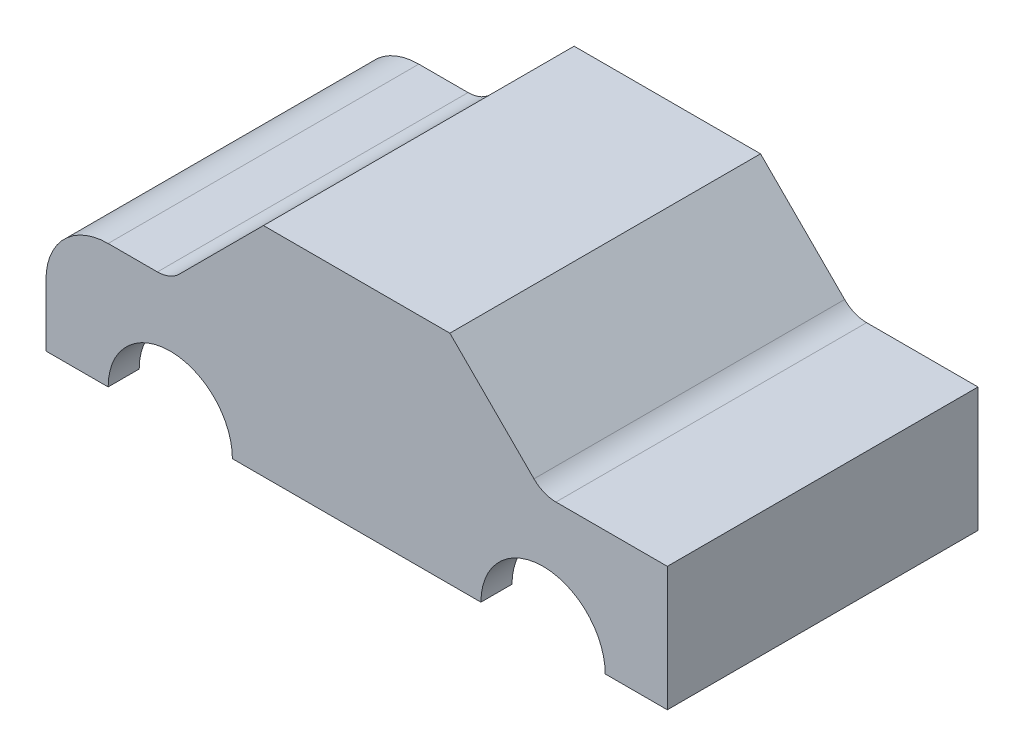
SolidWorks part; units mm, degrees
ref_plane "Front Plane" through (0, 0, 0) normal (0, 0, 1) x (1, 0, 0)
ref_plane "Top Plane" through (0, 0, 0) normal (0, 1, 0) x (1, 0, 0)
ref_plane "Right Plane" through (0, 0, 0) normal (1, 0, 0) x (0, 0, -1)
sketch "Sketch1" plane through (0, 0, 0) normal (0, 0, 1) x (1, 0, 0)
  line L0 (-50, 0) -> (50, 0)
  line L1 (50, 0) -> (50, 20)
  line L2 (50, 20) -> (32.0711, 20)
  line L3 (28.5355, 21.4645) -> (15, 35)
  line L4 (15, 35) -> (-15, 35)
  line L5 (-15, 35) -> (-28.5355, 21.4645)
  line L6 (-50, 0) -> (-50, 10)
  line L7 (-40, 20) -> (-32.0711, 20)
  arc A0 (-50, 10) -> (-40, 20) centre (-40, 10) cw
  arc A1 (32.0711, 20) -> (28.5355, 21.4645) centre (32.0711, 25) cw
  arc A2 (-28.5355, 21.4645) -> (-32.0711, 20) centre (-32.0711, 25) cw
  point P14 (30, 20)
  point P17 (-30, 20)
  dimension "D8" = 10
  dimension "D9" = 5
  dimension "D1" = 100
  dimension "D2" = 20
  dimension "D3" = 20
  dimension "D4" = 45
  dimension "D5" = 30
  dimension "D6" = 135
  dimension "D7" = 15
extrude "Boss-Extrude1" add sketch "Sketch1" along normal blind 50
shell "Shell1" thickness 5
sketch "Sketch2" plane through (0, 0, 50) normal (0, 0, 1) x (1, 0, 0)
  line L0 (-50, 0) -> (50, 0) construction
  line L1 (-50, 10) -> (-50, 0) construction
  line L2 (50, 0) -> (50, 20) construction
  line L3 (-40, 0) -> (-20, 0)
  line L4 (20, 0) -> (40, 0)
  arc A0 (-40, 0) -> (-20, 0) centre (-30, 0) cw
  arc A1 (20, 0) -> (40, 0) centre (30, 0) cw
  dimension "D1" = 10
  dimension "D3" = 20
  dimension "D4" = 10
  dimension "D2" = 10
extrude "Cut-Extrude1" cut sketch "Sketch2" against normal through all
sketch "Sketch5" plane through (0, 0, 0) normal (0, -1, 0) x (1, 0, 0)
  line L0 (-50, 50) -> (-40, 50) construction
  line L1 (-50, 0) -> (-40, 0) construction
  line L2 (-40, 0) -> (-40, 5) construction
  line L3 (-40, 45) -> (-40, 50) construction
  line L4 (50, 50) -> (50, 0) construction
  circle A0 centre (-45, 3) radius 0.75
  circle A1 centre (-45, 3) radius 1.5
  circle A2 centre (45, 3) radius 1.5
  circle A3 centre (45, 3) radius 0.75
  circle A4 centre (45, 47) radius 1.5
  circle A5 centre (45, 47) radius 0.75
  circle A6 centre (-45, 47) radius 1.5
  circle A7 centre (-45, 47) radius 0.75
  dimension "D1" = 1.5
  dimension "D2" = 3
  dimension "D3" = 5
  dimension "D4" = 3
  dimension "D7" = 3
  dimension "D8" = 5
  dimension "D9" = 5
  dimension "D5" = 2
  dimension "D6" = 2
extrude "Cut-Extrude3" cut sketch "Sketch5" against normal blind 5
sketch "Sketch6" plane through (0, 15, 0) normal (0, -1, 0) x (1, 0, 0)
  line L0 (30, -6.8205) -> (30, 65.9464) construction
  line L1 (50, 50) -> (50, 0) construction
  line L2 (50, 25) -> (-4.4509, 25) construction
  line L3 (35.25, 19.5) -> (35.25, 30.5)
  line L4 (43.25, 30.5) -> (16.75, 30.5)
  line L5 (43.25, 30.5) -> (43.25, 19.5)
  line L6 (43.25, 19.5) -> (16.75, 19.5)
  line L7 (16.75, 30.5) -> (16.75, 19.5)
  line L8 (43.25, 30.5) -> (16.75, 19.5) construction
  line L9 (43.25, 19.5) -> (16.75, 30.5) construction
  line L10 (18.25, 19.5) -> (18.25, 30.5)
  point P6 (30, 25)
  dimension "D1" = 20
  dimension "D2" = 11
  dimension "D3" = 26.5
  dimension "D4" = 8
  dimension "D5" = 1.5
extrude "Boss-Extrude2" add sketch "Sketch6" along normal blind 7.5 contours L6 L10 L4 L7 | L6 L5 L4 L3
sketch "Sketch7" plane through (0, 7.5, 0) normal (0, -1, 0) x (1, 0, 0)
  line L1 (43.25, 19.5) -> (35.25, 19.5)
  line L2 (43.25, 19.5) -> (43.25, 30.5)
  line L3 (43.25, 30.5) -> (35.25, 30.5)
  line L4 (35.25, 19.5) -> (35.25, 30.5)
sketch "Sketch8" plane through (0, 7.5, 0) normal (0, -1, 0) x (1, 0, 0)
  line L1 (43.25, 19.5) -> (35.25, 19.5)
  line L2 (43.25, 19.5) -> (43.25, 30.5)
  line L3 (43.25, 30.5) -> (35.25, 30.5)
  line L4 (35.25, 19.5) -> (35.25, 30.5)
extrude "Cut-Extrude5" cut sketch "Sketch8" against normal blind 3.5
